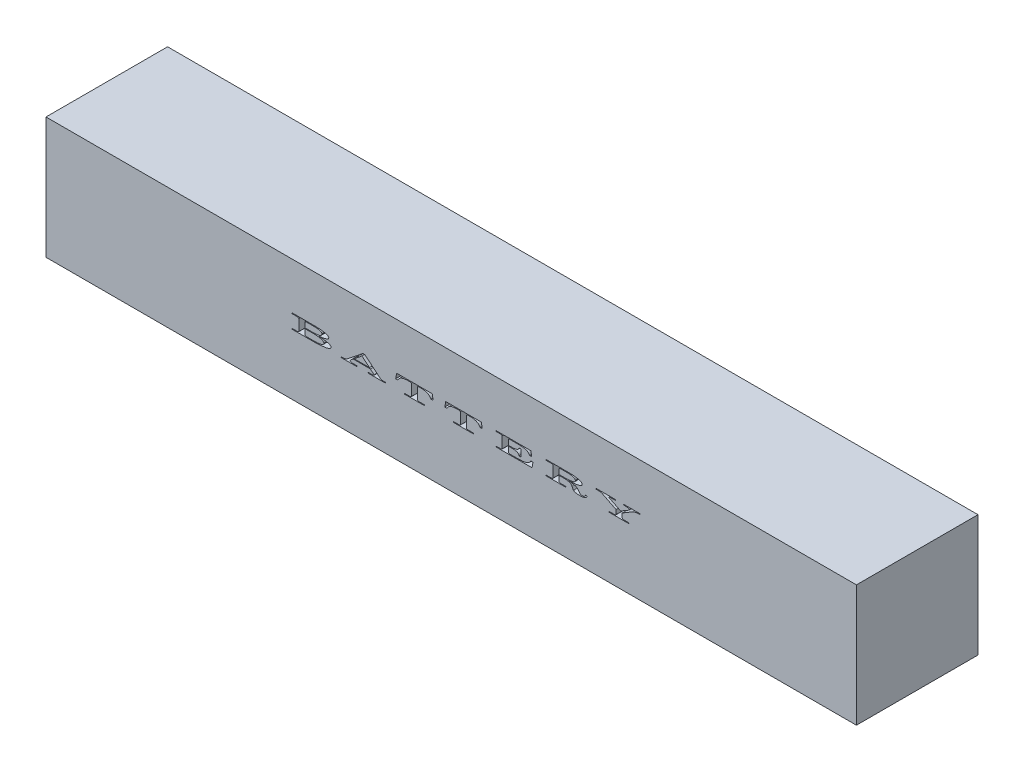
SolidWorks part; units mm, degrees
ref_plane "Front Plane" through (0, 0, 0) normal (0, 0, 1) x (1, 0, 0)
ref_plane "Top Plane" through (0, 0, 0) normal (0, 1, 0) x (1, 0, 0)
ref_plane "Right Plane" through (0, 0, 0) normal (1, 0, 0) x (0, 0, -1)
sketch "Sketch1" plane through (0, 0, 0) normal (0, 0, 1) x (1, 0, 0)
  line L1 (-100, 15) -> (100, 15)
  line L2 (-100, 15) -> (-100, -15)
  line L3 (-100, -15) -> (100, -15)
  line L4 (100, 15) -> (100, -15)
  line L5 (-100, 15) -> (100, -15) construction
  line L6 (-100, -15) -> (100, 15) construction
  point P0 (0, 0)
  dimension "D1" = 30
  dimension "D2" = 200
extrude "Boss-Extrude1" add sketch "Sketch1" along normal blind 30
sketch "Sketch2" plane through (0, 0, 30) normal (0, 0, 1) x (1, 0, 0)
  line L0 (-100, 15) -> (-100, -15) construction
  line L1 (100, 15) -> (-100, 15) construction
  text T0 "BATTERY" font "Century Schoolbook" height 3.5
  dimension "D1" = 60
  dimension "D2" = 15
extrude "Cut-Extrude1" cut sketch "Sketch2" against normal blind 5
